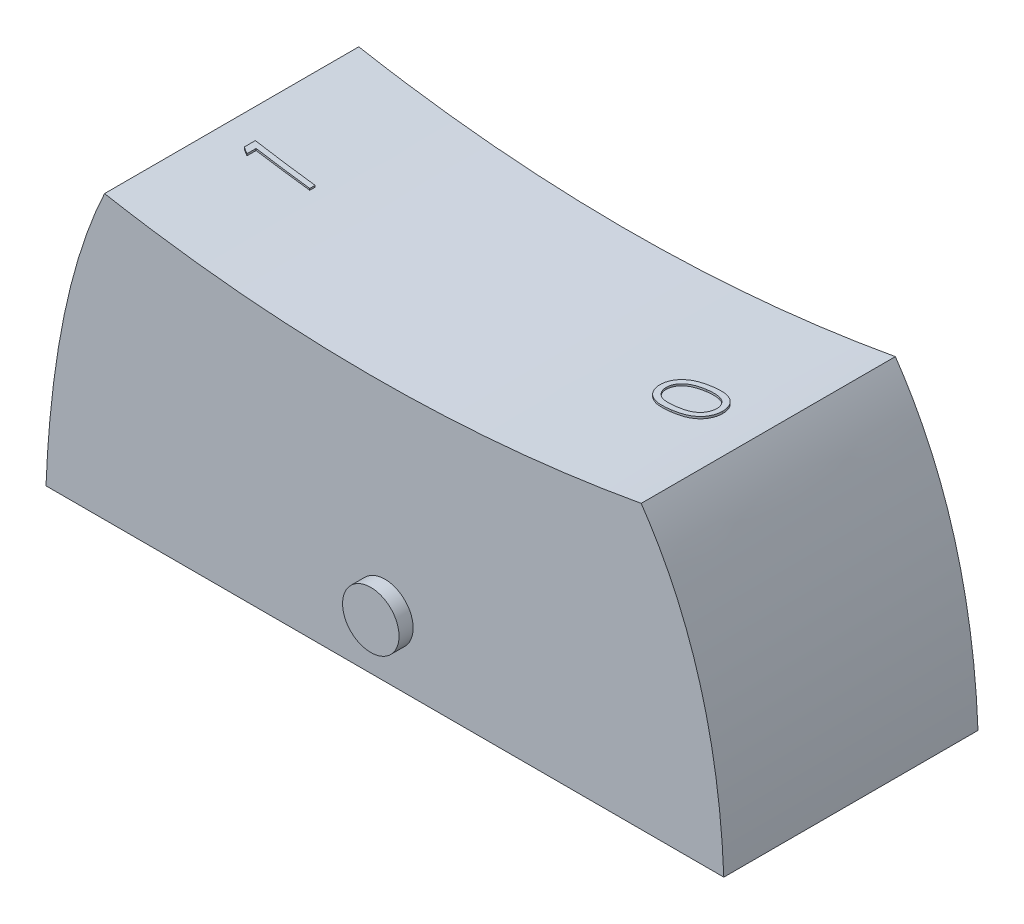
SolidWorks part; units mm, degrees
ref_plane "Front Plane" through (0, 0, 0) normal (0, 0, 1) x (1, 0, 0)
ref_plane "Top Plane" through (0, 0, 0) normal (0, 1, 0) x (1, 0, 0)
ref_plane "Right Plane" through (0, 0, 0) normal (1, 0, 0) x (0, 0, -1)
sketch "Sketch1" plane through (0, 0, 0) normal (0, 0, 1) x (1, 0, 0)
  line L3 (-12, -5) -> (12, -5)
  spline S0 degree 2 poles (-9.9263, 5) (-11.7528, 1.1056) (-12, -5) knots 0 0 0 1 1 1
  spline S1 degree 2 poles (9.0737, 5) (11.7528, 1.1056) (12, -5) knots 0 0 0 1 1 1
  spline S2 degree 2 poles (-9.9263, 5) (-0.4263, 3.2747) (9.0737, 5) knots 0 0 0 1 1 1
  point P0 (0, 0)
extrude "Boss-Extrude1" add sketch "Sketch1" along normal mid plane 9
sketch "Sketch2" plane through (0, 0, 0) normal (0, 0, 1) x (1, 0, 0)
  line L0 (-0.031, 4.1389) -> (-13.0845, 4.1389) construction
  circle A0 centre (0, -2.8611) radius 1
  parabola Q2 (9.0737, 5) -> (-9.9263, 5) focus (-0.4263, 30.2926) apex (-0.4263, 4.1374) construction
  dimension "D1" = 2
  dimension "D2" = 7
extrude "Boss-Extrude2" add sketch "Sketch2" along normal mid plane 10
sketch "Sketch3" plane through (0, 0, 0) normal (0, 1, 0) x (1, 0, 0)
  text T0 "<r90>1</r>" font "Century Gothic" height in points 8
extrude "Boss-Extrude3" add sketch "Sketch3" along normal blind 5
sketch "Sketch4" plane through (0, 0, 0) normal (0, 1, 0) x (1, 0, 0)
  text T0 "<r90>0</r>" font "Century Gothic" height in points 8
extrude "Boss-Extrude4" add sketch "Sketch4" along normal blind 5
sketch "Sketch5" plane through (0, 0, 4.5) normal (0, 0, 1) x (1, 0, 0)
  line L0 (-9.9041, 5.0684) -> (-7.7574, 6.0733)
  line L1 (-7.7574, 6.0733) -> (7.6612, 5.8153)
  line L2 (7.6612, 5.8153) -> (9.0412, 5.079)
  spline S0 degree 2 poles (-9.9041, 5.0684) (-0.4229, 3.2939) (9.0412, 5.079) knots 0 0 0 1 1 1
extrude "Cut-Extrude1" cut sketch "Sketch5" against normal through all
